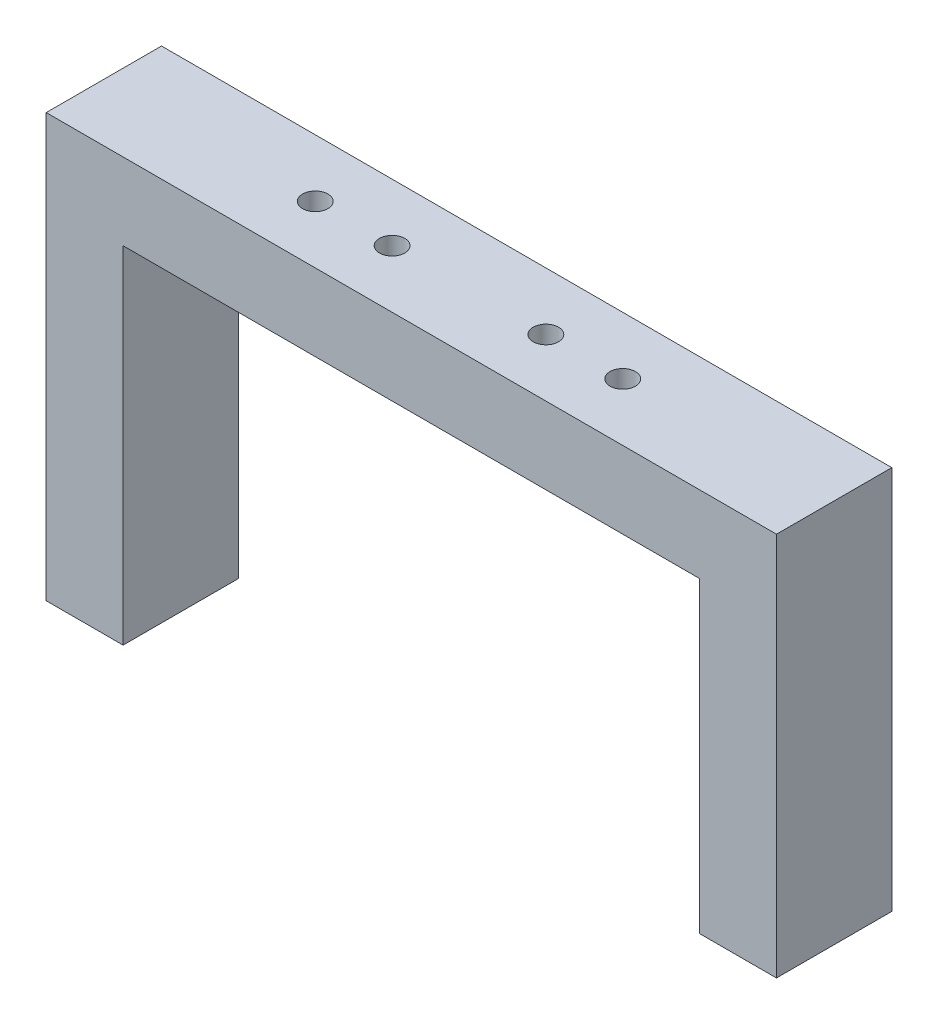
SolidWorks part; units mm, degrees
ref_plane "Front Plane" through (0, 0, 0) normal (0, 0, 1) x (1, 0, 0)
ref_plane "Top Plane" through (0, 0, 0) normal (0, 1, 0) x (1, 0, 0)
ref_plane "Right Plane" through (0, 0, 0) normal (1, 0, 0) x (0, 0, -1)
sketch "Sketch1" plane through (0, 0, 0) normal (0, 0, 1) x (1, 0, 0)
  line L0 (-37.5, 0) -> (37.5, 0)
  line L1 (-37.5, 0) -> (-37.5, -45)
  line L2 (37.5, 0) -> (37.5, -40)
  line L3 (47.5, 10) -> (47.5, -40)
  line L4 (-47.5, 10) -> (47.5, 10)
  line L5 (-47.5, 10) -> (-47.5, -45)
  line L6 (-37.5, -45) -> (-47.5, -45)
  line L7 (37.5, -40) -> (47.5, -40)
  point P3 (0, 0)
  dimension "D1" = 75
  dimension "D2" = 40
  dimension "D3" = 45
  dimension "D4" = 10
extrude "Boss-Extrude1" add sketch "Sketch1" along normal mid plane 15
sketch "Sketch2" plane through (0, 10, 0) normal (0, 1, 0) x (1, 0, 0)
  line L0 (-47.5, 0) -> (47.5, 0) construction
  line L1 (-47.5, -7.5) -> (-47.5, 7.5) construction
  line L2 (47.5, -7.5) -> (47.5, 7.5) construction
  circle A0 centre (-10, 0) radius 1.65
  circle A1 centre (10, 0) radius 1.65
  circle A2 centre (20, 0) radius 1.65
  circle A3 centre (-20, 0) radius 1.65
  point P14 (0, 0)
  dimension "D5" = 3.3
  dimension "D6" = 3.3
  dimension "D7" = 3.3
  dimension "D8" = 3.3
  dimension "D1" = 10
  dimension "D2" = 10
  dimension "D3" = 20
  dimension "D4" = 20
extrude "Cut-Extrude1" cut sketch "Sketch2" against normal up to next
